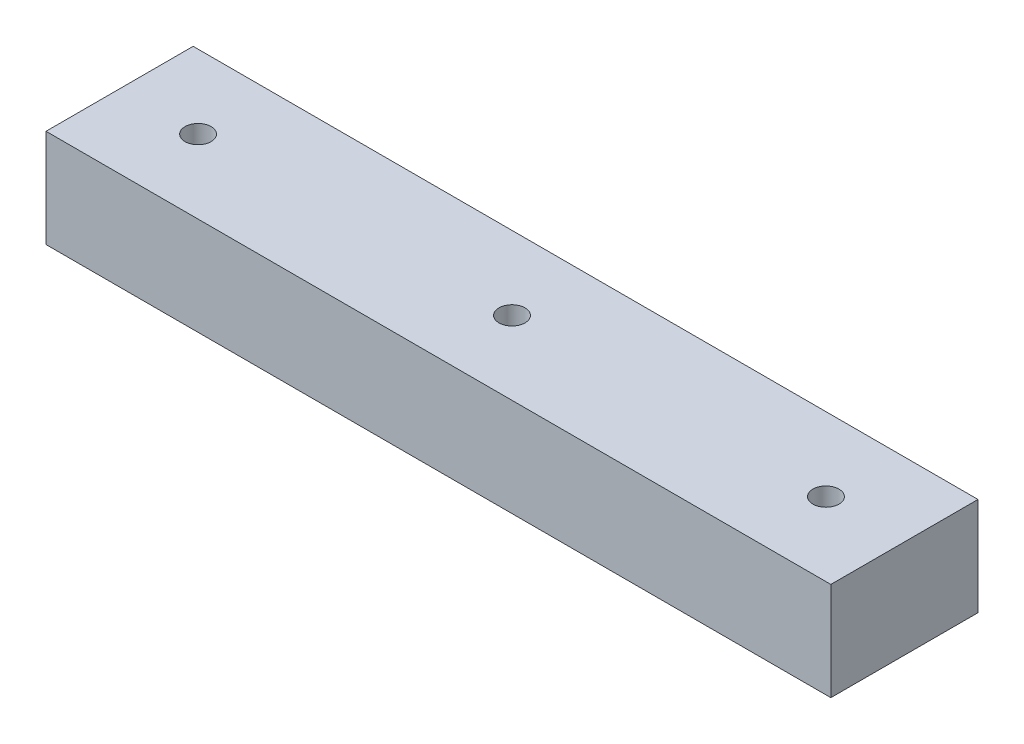
SolidWorks part; units mm, degrees
material "PPE"
ref_plane "Front Plane" through (0, 0, 0) normal (0, 0, 1) x (1, 0, 0)
ref_plane "Top Plane" through (0, 0, 0) normal (0, 1, 0) x (1, 0, 0)
ref_plane "Right Plane" through (0, 0, 0) normal (1, 0, 0) x (0, 0, -1)
sketch "Sketch1" plane through (0, 0, 0) normal (0, 1, 0) x (1, 0, 0)
  line L1 (-101.6, -19.05) -> (101.6, -19.05)
  line L2 (-101.6, -19.05) -> (-101.6, 19.05)
  line L3 (-101.6, 19.05) -> (101.6, 19.05)
  line L4 (101.6, -19.05) -> (101.6, 19.05)
  line L5 (-101.6, -19.05) -> (101.6, 19.05) construction
  line L6 (-101.6, 19.05) -> (101.6, -19.05) construction
  point P0 (0, 0)
  dimension "D1" = 203.2
  dimension "D2" = 38.1
extrude "Boss-Extrude1" add sketch "Sketch1" along normal blind 25.4
sketch "Sketch2" plane through (0, 25.4, 0) normal (0, 1, 0) x (1, 0, 0)
  line L0 (101.6, 19.05) -> (-101.6, 19.05) construction
  line L4 (-101.6, 19.05) -> (-101.6, -19.05) construction
  line L5 (0, 19.05) -> (0, -19.05) construction
  line L6 (-101.6, -19.05) -> (101.6, -19.05) construction
  circle A2 centre (0, 0) radius 3.3782
  circle A3 centre (-81.28, 0) radius 3.3782
  circle A4 centre (81.28, 0) radius 3.3782
  dimension "D2" = 19.05
  dimension "D1" = 6.7564
  dimension "D4" = 6.7564
  dimension "D3" = 101.6
  dimension "D5" = 19.05
  dimension "D6" = 20.32
extrude "Cut-Extrude1" cut sketch "Sketch2" against normal through all
scale "Scale1" [suppressed]
